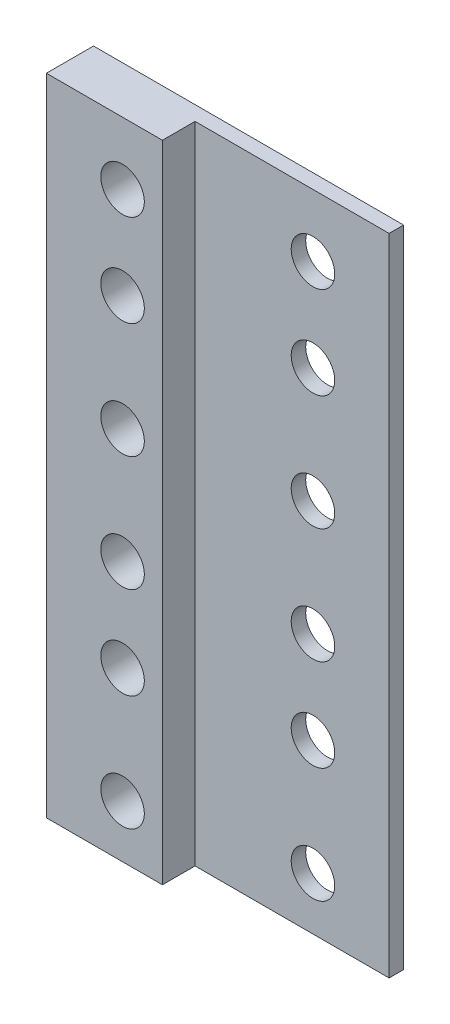
SolidWorks part; units mm, degrees
ref_plane "Front Plane" through (0, 0, 0) normal (0, 0, 1) x (1, 0, 0)
ref_plane "Top Plane" through (0, 0, 0) normal (0, 1, 0) x (1, 0, 0)
ref_plane "Right Plane" through (0, 0, 0) normal (1, 0, 0) x (0, 0, -1)
sketch "Sketch1" plane through (0, 0, 0) normal (0, 0, 1) x (1, 0, 0)
  line L0 (0, 88.9) -> (0, 0) construction
  line L2 (-25.25, 0) -> (17.5, 0)
  line L3 (-25.25, 0) -> (-25.25, 88.9)
  line L4 (-25.25, 88.9) -> (17.5, 88.9)
  line L5 (17.5, 0) -> (17.5, 88.9)
  line L6 (11.75, 62.84) -> (2.25, 62.84)
  line L7 (11.75, 72.34) -> (11.75, 62.84)
  line L12 (11.75, 85.04) -> (2.25, 85.04)
  line L13 (11.75, 85.04) -> (11.75, 75.54)
  line L33 (11.75, 75.54) -> (2.25, 75.54)
  line L34 (2.25, 85.04) -> (2.25, 75.54)
  line L35 (7, 75.54) -> (7, 85.04) construction
  line L36 (11.75, 80.29) -> (2.25, 80.29) construction
  line L37 (-10, 85.04) -> (-19.5, 85.04)
  line L38 (-10, 85.04) -> (-10, 75.54)
  line L39 (-10, 75.54) -> (-19.5, 75.54)
  line L40 (-19.5, 85.04) -> (-19.5, 75.54)
  line L41 (-14.75, 75.54) -> (-14.75, 85.04) construction
  line L42 (-10, 80.29) -> (-19.5, 80.29) construction
  line L43 (11.75, 72.34) -> (2.25, 72.34)
  line L44 (2.25, 72.34) -> (2.25, 62.84)
  line L45 (-10, 72.34) -> (-10, 62.84)
  line L46 (-10, 62.84) -> (-19.5, 62.84)
  line L47 (-10, 72.34) -> (-19.5, 72.34)
  line L48 (-19.5, 72.34) -> (-19.5, 62.84)
  line L73 (11.75, 50.14) -> (2.25, 50.14) [skipped]
  line L74 (11.75, 59.64) -> (11.75, 50.14) [skipped]
  line L75 (11.75, 59.64) -> (2.25, 59.64) [skipped]
  line L76 (2.25, 59.64) -> (2.25, 50.14) [skipped]
  line L77 (-10, 59.64) -> (-10, 50.14) [skipped]
  line L78 (-10, 50.14) -> (-19.5, 50.14) [skipped]
  line L79 (-10, 59.64) -> (-19.5, 59.64) [skipped]
  line L80 (-19.5, 59.64) -> (-19.5, 50.14) [skipped]
  line L81 (11.75, 37.44) -> (2.25, 37.44) [skipped]
  line L82 (11.75, 46.94) -> (11.75, 37.44) [skipped]
  line L83 (11.75, 46.94) -> (2.25, 46.94) [skipped]
  line L84 (2.25, 46.94) -> (2.25, 37.44) [skipped]
  line L85 (-10, 46.94) -> (-10, 37.44) [skipped]
  line L86 (-10, 37.44) -> (-19.5, 37.44) [skipped]
  line L87 (-10, 46.94) -> (-19.5, 46.94) [skipped]
  line L88 (-19.5, 46.94) -> (-19.5, 37.44) [skipped]
  line L89 (11.75, 24.74) -> (2.25, 24.74) [skipped]
  line L90 (11.75, 34.24) -> (11.75, 24.74) [skipped]
  line L91 (11.75, 34.24) -> (2.25, 34.24) [skipped]
  line L92 (2.25, 34.24) -> (2.25, 24.74) [skipped]
  line L93 (-10, 34.24) -> (-10, 24.74) [skipped]
  line L94 (-10, 24.74) -> (-19.5, 24.74) [skipped]
  line L95 (-10, 34.24) -> (-19.5, 34.24) [skipped]
  line L96 (-19.5, 34.24) -> (-19.5, 24.74) [skipped]
  line L97 (-19.5, 2.5) -> (-10, 2.5)
  line L98 (2.25, 46.96) -> (11.75, 46.96)
  line L99 (2.25, 46.96) -> (2.25, 56.46)
  line L100 (2.25, 56.46) -> (11.75, 56.46)
  line L101 (11.75, 46.96) -> (11.75, 56.46)
  line L102 (2.25, 46.96) -> (11.75, 56.46) construction
  line L103 (2.25, 56.46) -> (11.75, 46.96) construction
  line L104 (-19.5, 46.96) -> (-10, 46.96)
  line L105 (-19.5, 46.96) -> (-19.5, 56.46)
  line L106 (-19.5, 56.46) -> (-10, 56.46)
  line L107 (-10, 46.96) -> (-10, 56.46)
  line L108 (-19.5, 46.96) -> (-10, 56.46) construction
  line L109 (-19.5, 56.46) -> (-10, 46.96) construction
  line L110 (-19.5, 2.5) -> (-19.5, 12)
  line L111 (-19.5, 12) -> (-10, 12)
  line L112 (-10, 2.5) -> (-10, 12)
  line L113 (2.25, 2.5) -> (2.25, 12)
  line L114 (2.25, 2.5) -> (11.75, 2.5)
  line L115 (11.75, 2.5) -> (11.75, 12)
  line L116 (2.25, 12) -> (11.75, 12)
  line L117 (11.75, 18.38) -> (2.25, 18.38)
  line L118 (2.25, 27.88) -> (2.25, 18.38)
  line L119 (-10, 27.88) -> (-10, 18.38)
  line L120 (-10, 18.38) -> (-19.5, 18.38)
  line L121 (-19.5, 27.88) -> (-19.5, 18.38)
  line L122 (-10, 27.88) -> (-19.5, 27.88)
  line L123 (11.75, 27.88) -> (11.75, 18.38)
  line L124 (11.75, 27.88) -> (2.25, 27.88)
  line L125 (11.75, 31.08) -> (2.25, 31.08)
  line L126 (2.25, 40.58) -> (2.25, 31.08)
  line L127 (11.75, 40.58) -> (2.25, 40.58)
  line L128 (11.75, 40.58) -> (11.75, 31.08)
  line L129 (-10, 31.08) -> (-19.5, 31.08)
  line L130 (-19.5, 40.58) -> (-19.5, 31.08)
  line L131 (-10, 40.58) -> (-19.5, 40.58)
  line L132 (-10, 40.58) -> (-10, 31.08)
  point P2 (7, 51.71)
  point P27 (-14.75, 51.71)
  point P32 (-14.75, 46.96)
  point P195 (-14.75, 80.29)
  point P287 (7, 80.29)
  dimension "D1" = 88.9
  dimension "D2" = 2.25
  dimension "D3" = 5.75
  dimension "D4" = 3.86
  dimension "D5" = 10
  dimension "D6" = 9.5
  dimension "D7" = 9.5
  dimension "D8" = 3.86
  dimension "D10" = 9.5
  dimension "D9" = 9.5
  dimension "D11" = 5.75
  dimension "D12" = 5
  dimension "D13" = 3.2
  dimension "D14" = 9.5
  dimension "D15" = 9.5
  dimension "D16" = 6.38
  dimension "D17" = 2.25
  dimension "D18" = 9.5
  dimension "D19" = 9.5
  dimension "D20" = 6.38
  dimension "D21" = 10
  dimension "D23" = 6.38
  dimension "D22" = 2
extrude "Boss-Extrude1" add sketch "Sketch1" along normal blind 2
sketch "Sketch2" plane through (0, 0, 0) normal (0, 0, -1) x (-1, 0, 0)
  line L0 (-2.25, 85.04) -> (-2.25, 75.54) construction
  line L3 (-11.75, 85.04) -> (-2.25, 85.04) construction
  line L4 (-7, 80.29) -> (-7, 4.0252) construction
  line L5 (14.75, 80.29) -> (14.75, 4.0252) construction
  line L6 (-14.9582, 67.59) -> (32.2199, 67.59) construction
  line L7 (-14.9582, 51.71) -> (35.8343, 51.71) construction
  line L8 (-14.9582, 35.83) -> (28.9859, 35.83) construction
  line L9 (-14.9582, 23.13) -> (28.9859, 23.13) construction
  line L10 (-14.9582, 7.25) -> (28.9859, 7.25) construction
  line L11 (10, 62.84) -> (10, 72.34) construction
  line L12 (10, 72.34) -> (19.5, 72.34) construction
  line L13 (10, 56.46) -> (19.5, 56.46) construction
  line L14 (10, 40.58) -> (19.5, 40.58) construction
  line L15 (10, 27.88) -> (19.5, 27.88) construction
  line L16 (10, 12) -> (19.5, 12) construction
  line L17 (10, 85.04) -> (19.5, 85.04) construction
  line L19 (-11.75, 85.04) -> (-2.25, 85.04)
  line L20 (-11.75, 85.04) -> (-11.75, 75.54)
  line L21 (-11.75, 75.54) -> (-2.25, 75.54)
  line L22 (-2.25, 85.04) -> (-2.25, 75.54)
  line L23 (-7, 75.54) -> (-7, 85.04) construction
  line L24 (-11.75, 80.29) -> (-2.25, 80.29) construction
  line L25 (10, 85.04) -> (19.5, 85.04)
  line L26 (10, 85.04) -> (10, 75.54)
  line L27 (10, 75.54) -> (19.5, 75.54)
  line L28 (19.5, 85.04) -> (19.5, 75.54)
  line L29 (14.75, 75.54) -> (14.75, 85.04) construction
  line L30 (10, 80.29) -> (19.5, 80.29) construction
  line L31 (-11.75, 72.34) -> (-2.25, 72.34)
  line L32 (-11.75, 72.34) -> (-11.75, 62.84)
  line L33 (-11.75, 62.84) -> (-2.25, 62.84)
  line L34 (-2.25, 72.34) -> (-2.25, 62.84)
  line L35 (-7, 62.84) -> (-7, 72.34) construction
  line L36 (-11.75, 67.59) -> (-2.25, 67.59) construction
  line L37 (10, 72.34) -> (19.5, 72.34)
  line L38 (10, 72.34) -> (10, 62.84)
  line L39 (10, 62.84) -> (19.5, 62.84)
  line L40 (19.5, 72.34) -> (19.5, 62.84)
  line L41 (14.75, 62.84) -> (14.75, 72.34) construction
  line L42 (10, 67.59) -> (19.5, 67.59) construction
  line L43 (-11.75, 56.46) -> (-2.25, 56.46)
  line L44 (-11.75, 56.46) -> (-11.75, 46.96)
  line L45 (-11.75, 46.96) -> (-2.25, 46.96)
  line L46 (-2.25, 56.46) -> (-2.25, 46.96)
  line L47 (-7, 46.96) -> (-7, 56.46) construction
  line L48 (-11.75, 51.71) -> (-2.25, 51.71) construction
  line L49 (10, 56.46) -> (19.5, 56.46)
  line L50 (10, 56.46) -> (10, 46.96)
  line L51 (10, 46.96) -> (19.5, 46.96)
  line L52 (19.5, 56.46) -> (19.5, 46.96)
  line L53 (14.75, 46.96) -> (14.75, 56.46) construction
  line L54 (10, 51.71) -> (19.5, 51.71) construction
  line L55 (10, 46.96) -> (10, 56.46) construction
  line L56 (-11.75, 31.08) -> (-11.75, 40.58) construction
  line L57 (-11.75, 40.58) -> (-2.25, 40.58)
  line L58 (-11.75, 40.58) -> (-11.75, 31.08)
  line L59 (-11.75, 31.08) -> (-2.25, 31.08)
  line L60 (-2.25, 40.58) -> (-2.25, 31.08)
  line L61 (-7, 31.08) -> (-7, 40.58) construction
  line L62 (-11.75, 35.83) -> (-2.25, 35.83) construction
  line L64 (10, 40.58) -> (19.5, 40.58)
  line L65 (10, 40.58) -> (10, 31.08)
  line L66 (10, 31.08) -> (19.5, 31.08)
  line L67 (19.5, 40.58) -> (19.5, 31.08)
  line L68 (14.75, 31.08) -> (14.75, 40.58) construction
  line L69 (10, 35.83) -> (19.5, 35.83) construction
  line L70 (10, 31.08) -> (10, 40.58) construction
  line L72 (-11.75, 27.88) -> (-2.25, 27.88)
  line L73 (-11.75, 27.88) -> (-11.75, 18.38)
  line L74 (-11.75, 18.38) -> (-2.25, 18.38)
  line L75 (-2.25, 27.88) -> (-2.25, 18.38)
  line L76 (-7, 18.38) -> (-7, 27.88) construction
  line L77 (-11.75, 23.13) -> (-2.25, 23.13) construction
  line L78 (10, 27.88) -> (19.5, 27.88)
  line L79 (10, 27.88) -> (10, 18.38)
  line L80 (10, 18.38) -> (19.5, 18.38)
  line L81 (19.5, 27.88) -> (19.5, 18.38)
  line L82 (14.75, 18.38) -> (14.75, 27.88) construction
  line L83 (10, 23.13) -> (19.5, 23.13) construction
  line L84 (10, 12) -> (19.5, 12)
  line L85 (10, 12) -> (10, 2.5)
  line L86 (10, 2.5) -> (19.5, 2.5)
  line L87 (19.5, 12) -> (19.5, 2.5)
  line L88 (14.75, 2.5) -> (14.75, 12) construction
  line L89 (10, 7.25) -> (19.5, 7.25) construction
  line L90 (-11.75, 12) -> (-2.25, 12)
  line L91 (-11.75, 12) -> (-11.75, 2.5)
  line L92 (-11.75, 2.5) -> (-2.25, 2.5)
  line L93 (-2.25, 12) -> (-2.25, 2.5)
  line L94 (-7, 2.5) -> (-7, 12) construction
  line L95 (-11.75, 7.25) -> (-2.25, 7.25) construction
  circle A0 centre (-7, 80.29) radius 3
  circle A1 centre (14.75, 80.29) radius 3
  circle A2 centre (14.75, 67.59) radius 3
  circle A3 centre (-7, 67.59) radius 3
  circle A4 centre (-7, 51.71) radius 3
  circle A5 centre (14.75, 51.71) radius 3
  circle A6 centre (14.75, 35.83) radius 3
  circle A7 centre (14.75, 23.13) radius 3
  circle A8 centre (-7, 23.13) radius 3
  circle A9 centre (-7, 7.25) radius 3
  circle A10 centre (-7, 35.83) radius 3
  circle A11 centre (14.75, 7.25) radius 3
  point P148 (-7, 35.83)
  dimension "D2" = 4.75
  dimension "D3" = 6
  dimension "D10" = 6
  dimension "D12" = 6
  dimension "D13" = 6
  dimension "D14" = 6
  dimension "D15" = 6
  dimension "D16" = 6
  dimension "D17" = 6
  dimension "D18" = 6
  dimension "D19" = 6
  dimension "D20" = 6
  dimension "D21" = 6
  dimension "D1" = 4.75
  dimension "D4" = 4.75
  dimension "D5" = 4.75
  dimension "D6" = 4.75
  dimension "D7" = 4.75
  dimension "D8" = 4.75
  dimension "D9" = 4.75
  dimension "D11" = 4.75
  dimension "D22" = 9.5
  dimension "D23" = 9.5
  dimension "D24" = 9.5
  dimension "D25" = 9.5
  dimension "D26" = 9.5
  dimension "D27" = 9.5
  dimension "D28" = 9.5
  dimension "D29" = 9.5
  dimension "D30" = 9.5
  dimension "D31" = 9.5
extrude "Boss-Extrude2" add sketch "Sketch2" against normal blind 2
sketch "Sketch3" plane through (0, 0, 0) normal (0, 0, -1) x (-1, 0, 0)
  line L0 (-17.5, 88.9) -> (25.25, 88.9) construction
  line L1 (9.25, 88.9) -> (25.25, 88.9)
  line L2 (9.25, 88.9) -> (9.25, 0)
  line L3 (9.25, 0) -> (25.25, 0)
  line L4 (25.25, 88.9) -> (25.25, 0)
  line L5 (17.25, 0) -> (17.25, 88.9) construction
  line L6 (9.25, 44.45) -> (25.25, 44.45) construction
  circle A0 centre (14.75, 80.29) radius 3
  circle A1 centre (14.75, 67.59) radius 3
  circle A2 centre (14.75, 51.71) radius 3
  circle A3 centre (14.75, 35.83) radius 3
  circle A4 centre (14.75, 23.13) radius 3
  circle A5 centre (14.75, 7.25) radius 3
  point P260 (17.25, 44.45)
  dimension "D2" = 6
  dimension "D3" = 6
  dimension "D4" = 6
  dimension "D5" = 6
  dimension "D6" = 6
  dimension "D7" = 6
  dimension "D1" = 16
extrude "Boss-Extrude3" add sketch "Sketch3" against normal blind 6.5
